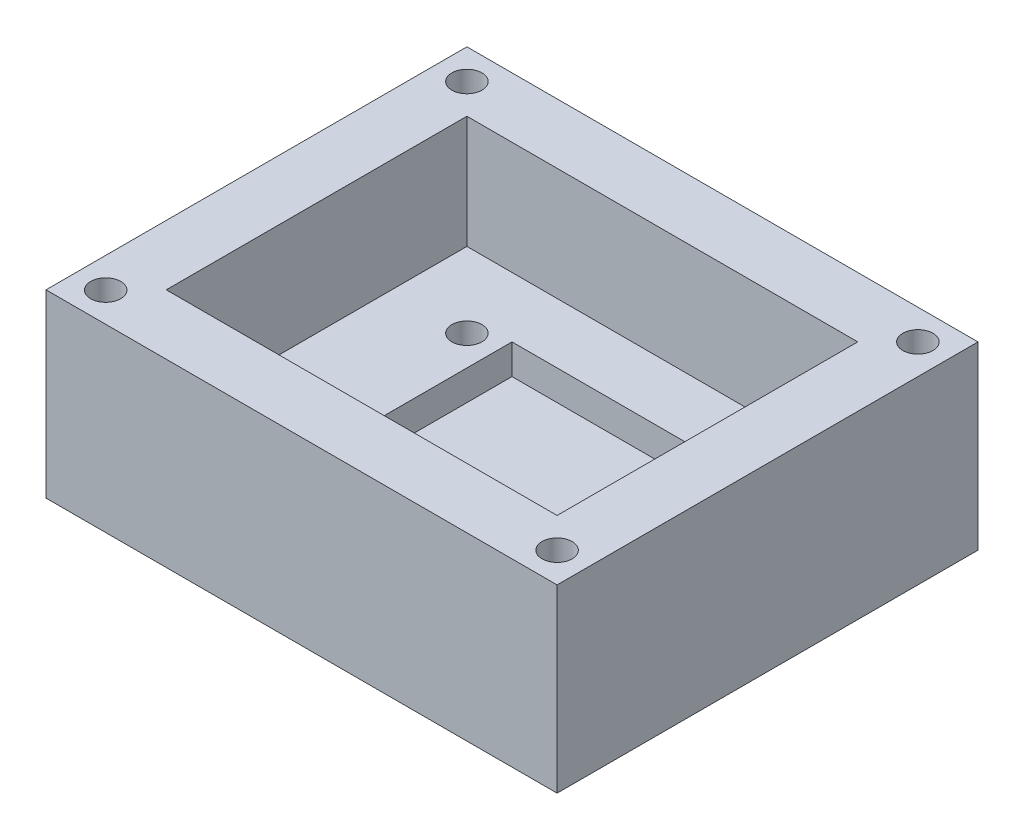
SolidWorks part; units mm, degrees
ref_plane "Front Plane" through (0, 0, 0) normal (0, 0, 1) x (1, 0, 0)
ref_plane "Top Plane" through (0, 0, 0) normal (0, 1, 0) x (1, 0, 0)
ref_plane "Right Plane" through (0, 0, 0) normal (1, 0, 0) x (0, 0, -1)
sketch "Sketch1" plane through (0, 0, 0) normal (0, 1, 0) x (1, 0, 0)
  line L1 (-16.6948, 8.7052) -> (26.4852, 8.7052)
  line L2 (-16.6948, 8.7052) -> (-16.6948, -26.8548)
  line L3 (-16.6948, -26.8548) -> (26.4852, -26.8548)
  line L4 (26.4852, 8.7052) -> (26.4852, -26.8548)
  dimension "D1" = 35.56
  dimension "D2" = 43.18
extrude "Boss-Extrude1" add sketch "Sketch1" along normal blind 15.24
sketch "Sketch2" plane through (0, 15.24, 0) normal (0, 1, 0) x (1, 0, 0)
  line L0 (-16.6948, 8.7052) -> (-16.6948, -26.8548) construction
  line L1 (-11.6148, 3.6252) -> (21.4052, 3.6252)
  line L2 (-11.6148, 3.6252) -> (-11.6148, -21.7748)
  line L3 (-11.6148, -21.7748) -> (21.4052, -21.7748)
  line L4 (21.4052, 3.6252) -> (21.4052, -21.7748)
  line L5 (-16.6948, -26.8548) -> (26.4852, -26.8548) construction
  dimension "D1" = 5.08
  dimension "D2" = 25.4
  dimension "1.1" = 33.02
  dimension ".2" = 5.08
extrude "Cut-Extrude1" cut sketch "Sketch2" against normal blind 9.525
sketch "Sketch4" plane through (0, 5.715, 0) normal (0, 1, 0) x (1, 0, 0)
  line L0 (21.4052, 3.6252) -> (-11.6148, 3.6252) construction
  line L1 (-2.7248, -1.4548) -> (12.5152, -1.4548)
  line L2 (-2.7248, -1.4548) -> (-2.7248, -16.6948)
  line L3 (-2.7248, -16.6948) -> (12.5152, -16.6948)
  line L4 (12.5152, -1.4548) -> (12.5152, -16.6948)
  line L5 (-11.6148, -21.7748) -> (21.4052, -21.7748) construction
  line L6 (-11.6148, 3.6252) -> (-11.6148, -21.7748) construction
  line L7 (21.4052, -21.7748) -> (21.4052, 3.6252) construction
  dimension "D1" = 5.08
  dimension "D2" = 5.08
  dimension "D3" = 8.89
  dimension "D4" = 8.89
extrude "Cut-Extrude2" cut sketch "Sketch4" against normal blind 2.54
sketch "Sketch7" plane through (0, 5.715, 0) normal (0, 1, 0) x (1, 0, 0)
  line L0 (21.4052, 3.6252) -> (-11.6148, 3.6252) construction
  line L1 (-11.6148, -21.7748) -> (21.4052, -21.7748) construction
  line L2 (-11.6148, 3.6252) -> (-11.6148, -21.7748) construction
  line L4 (-11.6148, 3.6252) -> (-11.6148, -21.7748) construction
  line L5 (21.4052, -21.7748) -> (21.4052, 3.6252) construction
  circle A0 centre (-5.2648, -2.7248) radius 1.27
  circle A1 centre (-5.2648, -15.4248) radius 1.27
  circle A2 centre (15.0552, -2.7248) radius 1.27
  circle A3 centre (15.0552, -15.4248) radius 1.27
  dimension "D1" = 6.35
  dimension "D3" = 6.35
  dimension "D2" = 6.35
  dimension "D4" = 6.35
  dimension "D5" = 6.35
  dimension "D6" = 6.35
extrude "Cut-Extrude3" cut sketch "Sketch7" against normal through all
sketch "Sketch8" plane through (0, 15.24, 0) normal (0, 1, 0) x (1, 0, 0)
  line L0 (26.4852, 8.7052) -> (-16.6948, 8.7052) construction
  line L1 (-16.6948, 8.7052) -> (-16.6948, -26.8548) construction
  line L2 (26.4852, -26.8548) -> (26.4852, 8.7052) construction
  line L3 (-16.6948, -26.8548) -> (26.4852, -26.8548) construction
  circle A0 centre (-14.1548, 6.1652) radius 1.27
  circle A1 centre (-14.1548, -24.3532) radius 1.27
  circle A2 centre (23.9452, 6.1652) radius 1.27
  circle A3 centre (23.9452, -24.3148) radius 1.27
  dimension "D1" = 2.54
  dimension "D2" = 2.54
  dimension "D3" = 2.54
  dimension "D4" = 2.54
  dimension "D5" = 2.54
  dimension "D6" = 2.54
  dimension "D7" = 2.54
extrude "Cut-Extrude4" cut sketch "Sketch8" against normal through all
